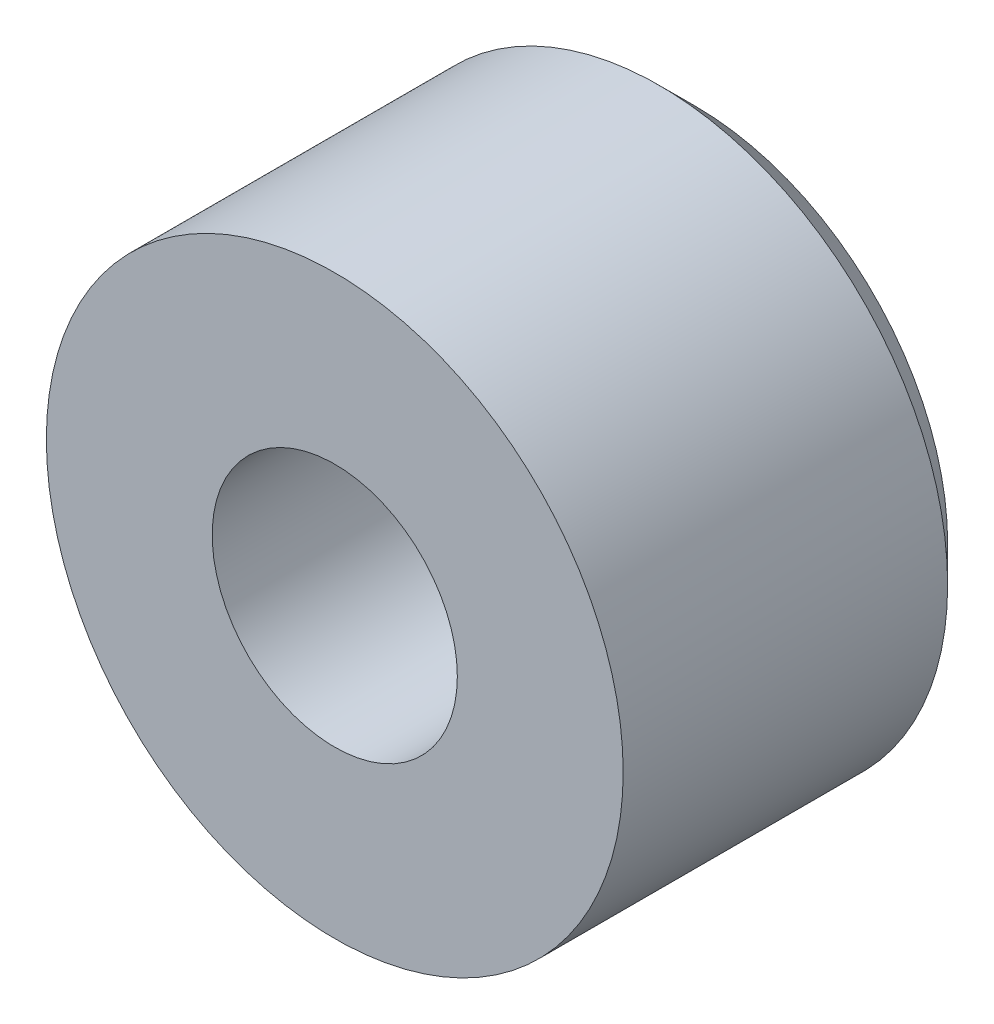
SolidWorks part; units mm, degrees
ref_plane "Top Plane" through (0, 0, 0) normal (0, 0, 1) x (1, 0, 0)
ref_plane "Front Plane" through (0, 0, 0) normal (0, 1, 0) x (1, 0, 0)
ref_plane "Right Plane" through (0, 0, 0) normal (1, 0, 0) x (0, 0, -1)
sketch "Sketch1" plane through (0, 0, 0) normal (0, 0, 1) x (1, 0, 0)
  circle A0 centre (0, 0) radius 1.7
  circle A1 centre (0, 0) radius 4
  dimension "D1" = 8
  dimension "D2" = 3.4
extrude "Boss-Extrude1" add sketch "Sketch1" along normal blind 5
chamfer "Chamfer1" distance 0.5 angle 45 2 edges at (1.7, 0, 0) (4, 0, 0)
